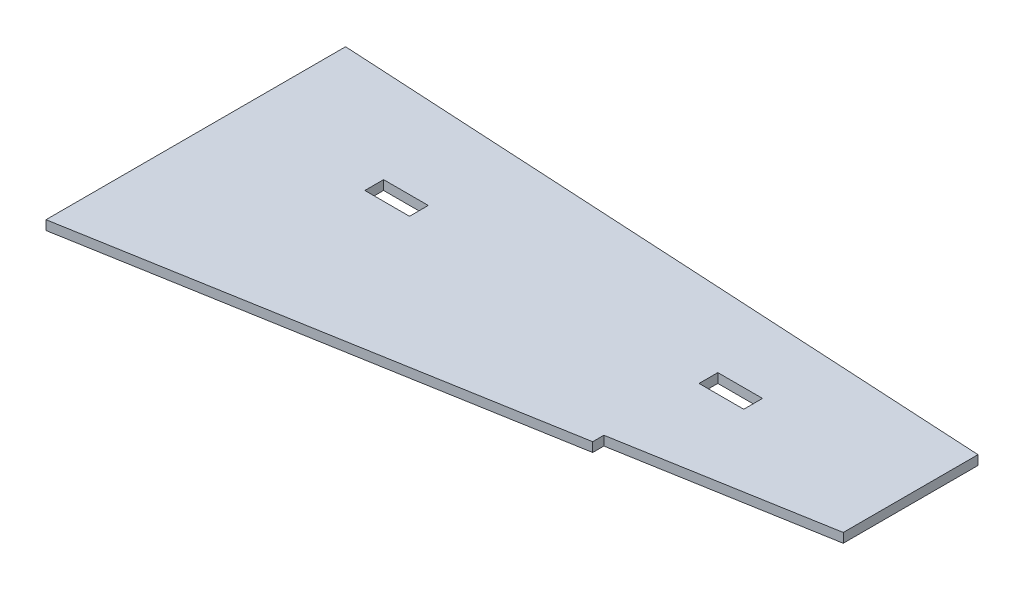
SolidWorks part; units mm, degrees
ref_plane "Front" through (0, 0, 0) normal (0, 0, 1) x (1, 0, 0)
ref_plane "Top" through (0, 0, 0) normal (0, 1, 0) x (1, 0, 0)
ref_plane "Right" through (0, 0, 0) normal (1, 0, 0) x (0, 0, -1)
sketch "Sketch1" plane through (0, 0, 0) normal (0, 1, 0) x (1, 0, 0)
  line L0 (602.1137, -343.7415) -> (602.1137, -2482.4082) construction
  line L1 (0, 0) -> (380.417, -21.0684)
  line L2 (0, 0) -> (0, -206.442) construction
  line L3 (380.417, -21.0684) -> (380.417, -97.6337)
  line L4 (264.5645, -124.1601) -> (0, -170.2354)
  line L5 (0, 0) -> (0, -170.2354)
  line L6 (380.417, -21.0684) -> (455.6706, -25.2362)
  line L7 (460.8009, -126.1911) -> (0, -206.442)
  line L8 (0, -170.2354) -> (0, -206.442)
  line L9 (272.8412, -158.9253) -> (272.8412, -130.6723)
  line L10 (272.8412, -130.6723) -> (455.1314, -98.9254)
  line L11 (455.1314, -98.9254) -> (455.1314, -127.1784)
  line L12 (264.5645, -124.1601) -> (264.5645, -117.8101)
  line L13 (264.5645, -117.8101) -> (380.417, -97.6337)
  spline S0 degree 3 poles (455.6706, -25.2362) (459.3541, -25.4402) (464.065, -27.4709) (469.9936, -39.0852) (473.4584, -72.4051) (464.1079, -102.8001) (460.8009, -126.1911) knots 0 0 0 0 0.082695 0.147079 0.342427 1 1 1 1
  dimension "D1" = 381
  dimension "D2" = 86.83
  dimension "D3" = 80.121
  dimension "D4" = 6.35
extrude "Base" add sketch "Sketch1" along normal blind 5.334 contours L1 L5 L4 L3
sketch "Folded Sketch" [suppressed] plane through (0, 5.334, 0) normal (0, 1, 0) x (1, 0, 0)
  line L0 (-24.2728, 0) -> (-24.2728, -206.5305) construction
  line L1 (0, 0) -> (380.417, -21.0684)
  line L2 (0, 0) -> (0, -206.442) construction
  line L3 (1.27, -44.45) -> (470.8001, -49.6152)
  line L4 (0.9116, -90.1699) -> (469.3093, -78.835)
  line L5 (0, 0) -> (0, -206.442)
  line L6 (380.417, -21.0684) -> (455.6706, -25.2362)
  line L7 (460.8009, -126.1911) -> (0, -206.442)
  line L8 (0, 0) -> (1.27, -44.45)
  line L9 (272.8412, -158.9253) -> (272.8412, -130.6723)
  line L10 (272.8412, -130.6723) -> (455.1314, -98.9254)
  line L11 (455.1314, -98.9254) -> (455.1314, -127.1784)
  line L12 (0, 0) -> (0, -170.2354) construction
  line L13 (1.27, -44.45) -> (0, -206.442)
  line L14 (0, 0) -> (502.0386, 0) construction
  spline S0 degree 3 poles (455.6706, -25.2362) (459.3541, -25.4402) (464.065, -27.4709) (469.9936, -39.0852) (473.4584, -72.4051) (464.1079, -102.8001) (460.8009, -126.1911) knots 0 0 0 0 0.082695 0.147079 0.342427 1 1 1 1
  dimension "D1" = 44.45
  dimension "D2" = 1.27
  dimension "D3" = 45.7213
ref_plane "Spacer Height " [suppressed] through (0, 18.034, 0) normal (0, 1, 0) x (1, 0, 0)
sketch "Sketch3" plane through (0, 0, 0) normal (0, -1, 0) x (1, 0, 0)
  line L8 (291.517, 54.6115) -> (291.517, 65.2795)
  line L9 (291.517, 65.2795) -> (266.117, 65.2795)
  line L10 (266.117, 65.2795) -> (266.117, 54.6115)
  line L11 (266.117, 54.6115) -> (291.517, 54.6115)
  line L12 (101.6, 54.6115) -> (101.6, 65.2795)
  line L13 (101.6, 65.2795) -> (76.2, 65.2795)
  line L14 (76.2, 65.2795) -> (76.2, 54.6115)
  line L15 (76.2, 54.6115) -> (101.6, 54.6115)
extrude "Cut-Extrude1" cut sketch "Sketch3" against normal up to next
sketch "Build Plans (Right Wing)" plane through (0, 0, 0) normal (0, 1, 0) x (1, 0, 0)
  line L0 (-24.2728, 0) -> (-24.2728, -206.5305) construction
  line L1 (0, 0) -> (380.417, -21.0684)
  line L5 (101.6, -54.6115) -> (101.6, -65.2795) construction
  line L6 (380.417, -21.0684) -> (455.6706, -25.2362)
  line L7 (76.2, -54.6115) -> (101.6, -54.6115) construction
  line L8 (76.2, -65.2795) -> (76.2, -54.6115) construction
  line L9 (101.6, -65.2795) -> (76.2, -65.2795) construction
  line L10 (266.117, -65.2795) -> (266.117, -54.6115) construction
  line L11 (266.117, -54.6115) -> (291.517, -54.6115) construction
  line L12 (291.517, -54.6115) -> (291.517, -65.2795) construction
  line L13 (463.2719, 48.062) -> (466.3918, 76.1422)
  line L14 (285.6022, 99.7443) -> (463.2719, 48.062)
  line L15 (288.7221, 127.8245) -> (285.6022, 99.7443)
  line L16 (471.9176, 74.5348) -> (22.7966, 205.1795)
  line L17 (10.8631, 89.5178) -> (475.1446, 26.5288)
  line L18 (6.1707, 44.0379) -> (22.7966, 205.1795)
  line L19 (0, 0) -> (6.1707, 44.0379)
  line L20 (6.1707, 44.0379) -> (473.3996, -2.6769)
  line L21 (291.517, -65.2795) -> (266.117, -65.2795) construction
  line L22 (291.517, -65.2795) -> (266.117, -65.2795)
  line L23 (291.517, -54.6115) -> (291.517, -65.2795)
  line L24 (266.117, -54.6115) -> (291.517, -54.6115)
  line L25 (266.117, -65.2795) -> (266.117, -54.6115)
  line L26 (101.6, -54.6115) -> (101.6, -65.2795)
  line L27 (101.6, -65.2795) -> (76.2, -65.2795)
  line L28 (76.2, -65.2795) -> (76.2, -54.6115)
  line L29 (76.2, -54.6115) -> (101.6, -54.6115)
  line L33 (264.5645, -124.1601) -> (264.5645, -117.8101)
  line L34 (264.5645, -117.8101) -> (380.417, -97.6337)
  line L35 (380.417, -97.6337) -> (380.417, -21.0684)
  line L36 (380.417, -21.0684) -> (0, 0)
  line L37 (0, 0) -> (0, -170.2354)
  line L38 (0, -170.2354) -> (264.5645, -124.1601)
  line L39 (264.5645, -124.1601) -> (264.5645, -117.8101)
  line L40 (264.5645, -117.8101) -> (380.417, -97.6337)
  line L41 (380.417, -97.6337) -> (380.417, -21.0684)
  line L42 (380.417, -21.0684) -> (0, 0)
  line L43 (0, 0) -> (0, -170.2354)
  line L44 (0, -170.2354) -> (264.5645, -124.1601)
  spline S1 degree 3 poles (455.6706, -25.2362) (459.3541, -25.4402) (464.2605, -23.9421) (471.4353, -13.0535) (478.5583, 19.68) (472.6214, 50.9217) (471.9176, 74.5348) knots 0 0 0 0 0.082695 0.147079 0.342427 1 1 1 1
  dimension "D1" = 0
sketch "Build Plans (Left Wing)" [suppressed] plane through (0, 0, 0) normal (0, 1, 0) x (1, 0, 0)
  line L0 (24.2728, 0) -> (24.2728, -206.5305) construction
  line L25 (0, -170.2354) -> (-264.5645, -124.1601)
  line L26 (0, 0) -> (0, -170.2354)
  line L27 (-380.417, -21.0684) -> (0, 0)
  line L28 (-380.417, -97.6337) -> (-380.417, -21.0684)
  line L29 (-264.5645, -117.8101) -> (-380.417, -97.6337)
  line L30 (-264.5645, -124.1601) -> (-264.5645, -117.8101)
  line L31 (-76.2, -54.6115) -> (-101.6, -54.6115)
  line L32 (-76.2, -65.2795) -> (-76.2, -54.6115)
  line L33 (-101.6, -65.2795) -> (-76.2, -65.2795)
  line L34 (-101.6, -54.6115) -> (-101.6, -65.2795)
  line L35 (-266.117, -65.2795) -> (-266.117, -54.6115)
  line L36 (-266.117, -54.6115) -> (-291.517, -54.6115)
  line L37 (-291.517, -54.6115) -> (-291.517, -65.2795)
  line L38 (-291.517, -65.2795) -> (-266.117, -65.2795)
  line L39 (-6.1707, 44.0379) -> (-473.3996, -2.6769)
  line L40 (0, 0) -> (-6.1707, 44.0379)
  line L41 (-6.1707, 44.0379) -> (-22.7966, 205.1795)
  line L42 (-10.8631, 89.5178) -> (-475.1446, 26.5288)
  line L43 (-471.9176, 74.5348) -> (-22.7966, 205.1795)
  line L44 (-288.7221, 127.8245) -> (-285.6022, 99.7443)
  line L45 (-285.6022, 99.7443) -> (-463.2719, 48.062)
  line L46 (-463.2719, 48.062) -> (-466.3918, 76.1422)
  line L47 (-380.417, -21.0684) -> (-455.6706, -25.2362)
  line L48 (0, 0) -> (-380.417, -21.0684)
  spline S1 degree 3 poles (-455.6706, -25.2362) (-459.3541, -25.4402) (-464.2605, -23.9421) (-471.4353, -13.0535) (-478.5583, 19.68) (-472.6214, 50.9217) (-471.9176, 74.5348) knots 0 0 0 0 0.082695 0.147079 0.342427 1 1 1 1
